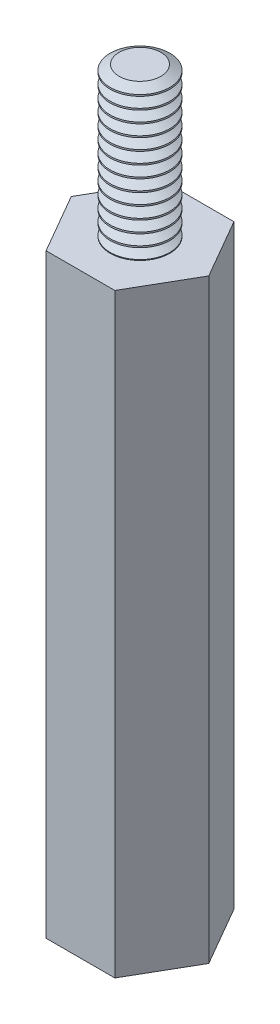
SolidWorks part; units mm, degrees
material "ABS"
ref_plane "Front Plane" through (0, 0, 0) normal (0, 0, 1) x (1, 0, 0)
ref_plane "Top Plane" through (0, 0, 0) normal (0, 1, 0) x (1, 0, 0)
ref_plane "Right Plane" through (0, 0, 0) normal (1, 0, 0) x (0, 0, -1)
sketch "Sketch1" plane through (0, 0, 0) normal (0, 1, 0) x (1, 0, 0)
  line L1 (2.3094, 0) -> (1.1547, 2)
  line L2 (1.1547, 2) -> (-1.1547, 2)
  line L3 (-1.1547, 2) -> (-2.3094, 0)
  line L4 (-2.3094, 0) -> (-1.1547, -2)
  line L5 (-1.1547, -2) -> (1.1547, -2)
  line L6 (1.1547, -2) -> (2.3094, 0)
  circle A0 centre (0, 0) radius 2 construction
  dimension "D1" = 4
extrude "Boss-Extrude1" add sketch "Sketch1" along normal blind 20
sketch "Sketch3" plane through (0, 0, 0) normal (0, -1, 0) x (1, 0, 0)
  circle A0 centre (0, 0) radius 0.8
  dimension "D1" = 1.6
extrude "Cut-Extrude1" cut sketch "Sketch3" against normal blind 6
sketch "Sketch2" plane through (0, 20, 0) normal (0, 1, 0) x (1, 0, 0)
  circle A0 centre (0, 0) radius 1
  dimension "D1" = 2
extrude "Boss-Extrude2" add sketch "Sketch2" along normal blind 5
sketch "Sketch5" plane through (0, 0, 0) normal (0, 0, 1) x (1, 0, 0)
  line L0 (0, 0) -> (0.38, 0) construction
  line L1 (0.38, 0) -> (0.78, 0) construction
  line L2 (0.78, 0) -> (1.1264, 0) construction
  line L3 (0.78, -0.2) -> (0.78, 0.2) construction
  line L4 (0.38, 0.2) -> (0.38, -0.2)
  line L5 (0.38, 0.2) -> (0.78, 0.2)
  line L6 (0.78, 0.2) -> (1.1264, 0)
  line L7 (1.1264, 0) -> (0.78, -0.2)
  line L8 (0.78, -0.2) -> (0.38, -0.2)
  line L9 (-0.8, 0) -> (0.8, 0) construction
  line L10 (0, 0) -> (0, 6) construction
  line L11 (-0.8, 6) -> (0.8, 6) construction
  dimension "D1" = 60
  dimension "D2" = 0.4
  dimension "D3" = 0.78
revolve "Cut-Revolve1" cut sketch "Sketch5" angle 360 about L10
pattern_linear "LPattern1" count 15 spacing 0.4 along (0, 1, 0) of "Cut-Revolve1"
sketch "Sketch6" plane through (0, 0, 0) normal (0, 0, 1) x (1, 0, 0)
  line L0 (0, 0) -> (0, 25) construction
  line L1 (1, 25) -> (-1, 25) construction
  line L2 (0, 25) -> (0.7, 25) construction
  line L3 (0.7, 25) -> (1.0464, 25) construction
  line L4 (1.0464, 25) -> (1.4464, 25) construction
  line L5 (1.4464, 25.2) -> (1.4464, 24.8)
  line L6 (1.0464, 25.2) -> (1.0464, 24.8) construction
  line L7 (1.4464, 25.2) -> (1.0464, 25.2)
  line L8 (1.0464, 25.2) -> (0.7, 25)
  line L9 (0.7, 25) -> (1.0464, 24.8)
  line L10 (1.0464, 24.8) -> (1.4464, 24.8)
  point P12 (1.0139, 25)
  dimension "D1" = 60
  dimension "D2" = 0.4
  dimension "D3" = 0.7
revolve "Cut-Revolve2" cut sketch "Sketch6" angle 360 about L0
pattern_linear "LPattern2" count 13 spacing 0.4 along (0, -1, 0) of "Cut-Revolve2"
